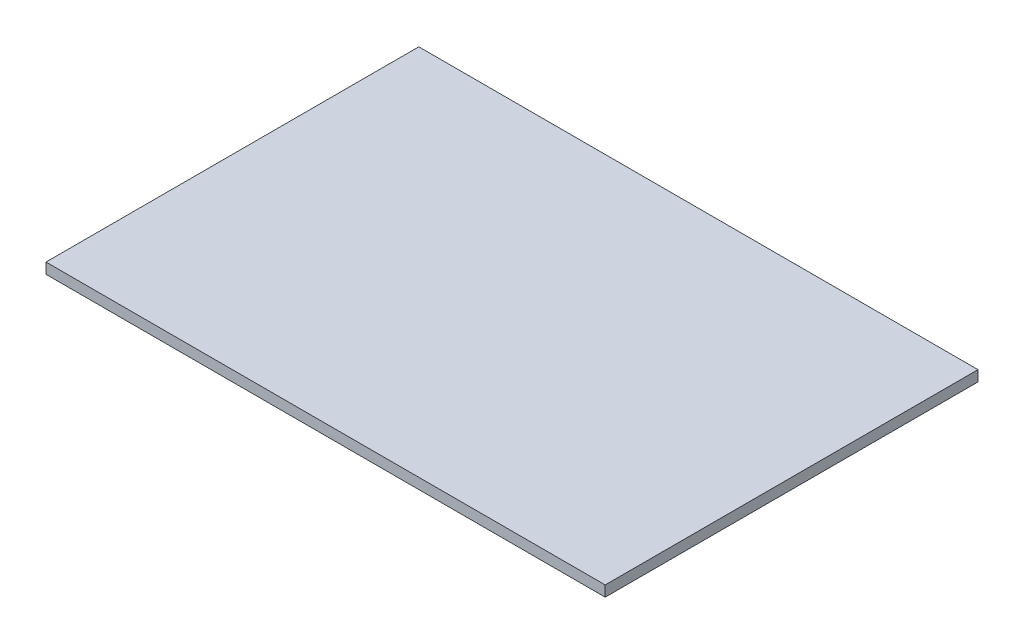
SolidWorks part; units mm, degrees
ref_plane "Front Plane" through (0, 0, 0) normal (0, 0, 1) x (1, 0, 0)
ref_plane "Top Plane" through (0, 0, 0) normal (0, 1, 0) x (1, 0, 0)
ref_plane "Right Plane" through (0, 0, 0) normal (1, 0, 0) x (0, 0, -1)
sketch "Sketch1" plane through (0, 0, 0) normal (0, 1, 0) x (1, 0, 0)
  line L1 (-52.5, 35) -> (52.5, 35)
  line L2 (-52.5, 35) -> (-52.5, -35)
  line L3 (-52.5, -35) -> (52.5, -35)
  line L4 (52.5, 35) -> (52.5, -35)
  line L5 (-52.5, 35) -> (52.5, -35) construction
  line L6 (-52.5, -35) -> (52.5, 35) construction
  point P0 (0, 0)
  dimension "D1" = 105
  dimension "D2" = 70
extrude "Boss-Extrude1" add sketch "Sketch1" along normal blind 2
